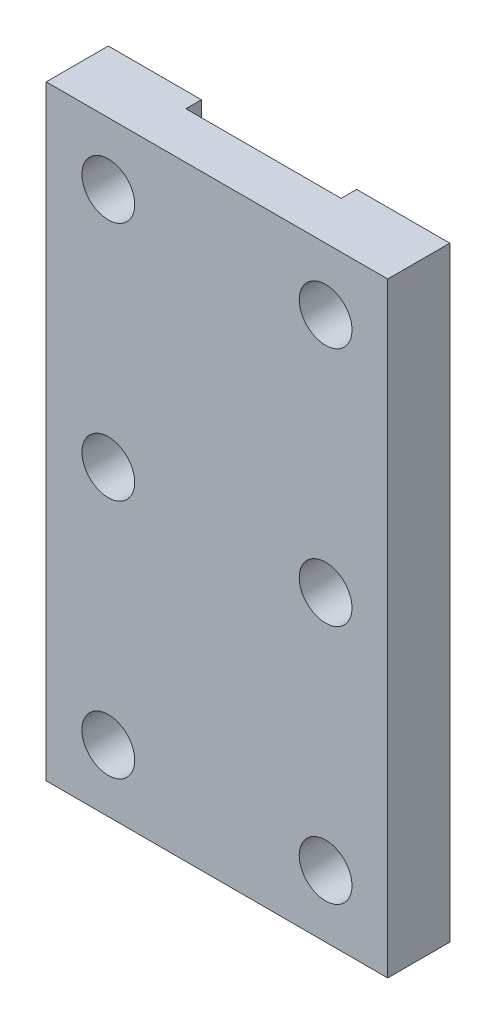
SolidWorks part; units mm, degrees
ref_plane "前基準面" through (0, 0, 0) normal (0, 0, 1) x (1, 0, 0)
ref_plane "上基準面" through (0, 0, 0) normal (0, 1, 0) x (1, 0, 0)
ref_plane "右基準面" through (0, 0, 0) normal (1, 0, 0) x (0, 0, -1)
sketch "草圖1" plane through (0, 0, 0) normal (0, 0, 1) x (1, 0, 0)
  line L1 (-11, 19.5) -> (11, 19.5)
  line L2 (-11, 19.5) -> (-11, -19.5)
  line L3 (-11, -19.5) -> (11, -19.5)
  line L4 (11, 19.5) -> (11, -19.5)
  line L5 (-11, 19.5) -> (11, -19.5) construction
  line L6 (-11, -19.5) -> (11, 19.5) construction
  point P0 (0, 0)
  dimension "D1" = 39
  dimension "D2" = 22
extrude "填料-伸長1" add sketch "草圖1" along normal blind 4
sketch "草圖2" plane through (0, 19.5, 0) normal (0, 1, 0) x (1, 0, 0)
  line L1 (-5, 0) -> (5, 0)
  line L2 (-5, 0) -> (-5, -1)
  line L3 (-5, -1) -> (5, -1)
  line L4 (5, 0) -> (5, -1)
  dimension "D1" = 1
  dimension "D2" = 10
extrude "除料-伸長1" cut sketch "草圖2" against normal through all
sketch "草圖3" plane through (0, 0, 0) normal (0, 0, -1) x (-1, 0, 0)
  line L0 (-7, 0) -> (-7, 15.5) construction
  line L1 (-7, 0) -> (0, 0) construction
  circle A0 centre (-7, 15.5) radius 1.7
  dimension "D3" = 3.4
  dimension "D1" = 7
  dimension "D2" = 15.5
extrude "除料-伸長2" cut sketch "草圖3" against normal through all
pattern_linear "直線複製排列1" count 2 spacing 14 along (-1, 0, 0) count 3 spacing 15.5 along (0, -1, 0) of "除料-伸長2"
